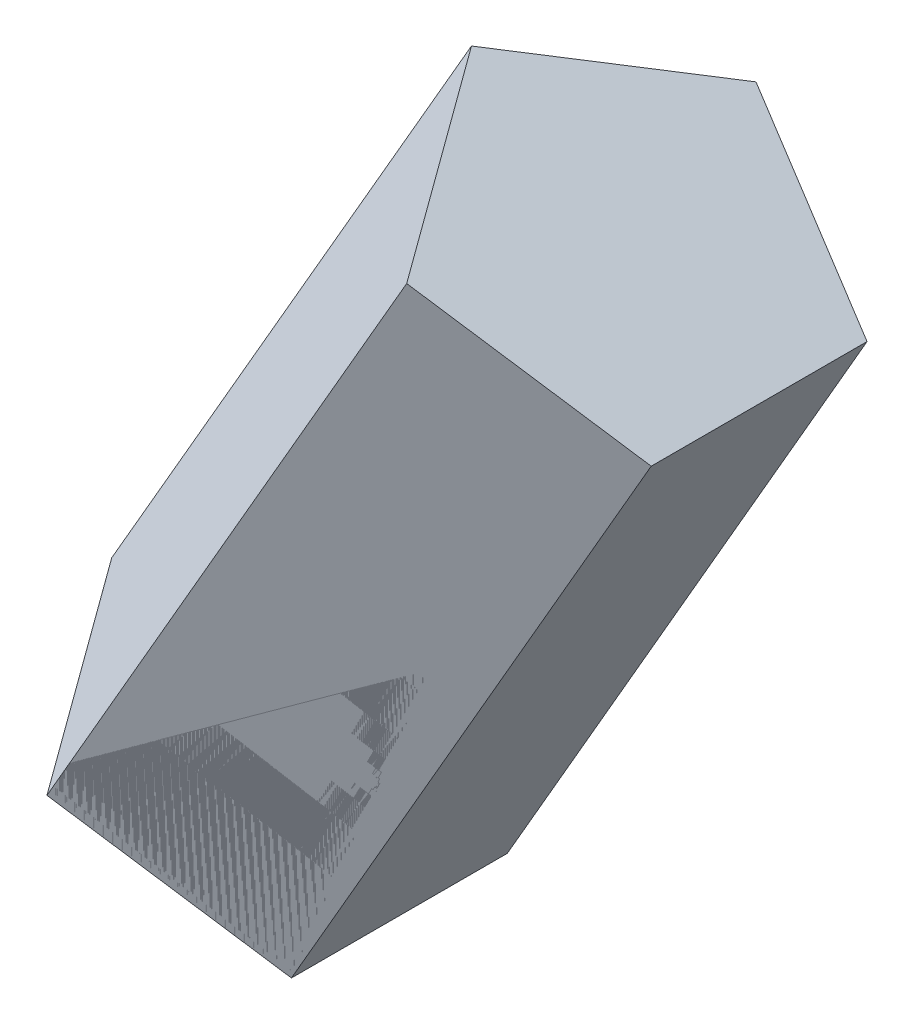
SolidWorks part; units mm, degrees
ref_plane "VP" through (0, 0, 0) normal (0, 0, 1) x (1, 0, 0)
ref_plane "HP" through (0, 0, 0) normal (0, 1, 0) x (1, 0, 0)
ref_plane "Right Plane" through (0, 0, 0) normal (1, 0, 0) x (0, 0, -1)
sketch "Sketch5" plane through (0, 0, 0) normal (0, 1, 0) x (1, 0, 0)
  line L0 (130, 0) -> (130, -60.0996) construction
  line L1 (-30.8326, 0) -> (30.8326, 0) construction
  dimension "D1" = 130
ref_plane "60 deg" through (32.5, 56.2917, 0) normal (-0.5, -0.866, 0) x (-0.866, 0.5, 0)
sketch "Sketch6" plane through (32.5, 56.2917, 0) normal (-0.5, -0.866, 0) x (-0.866, 0.5, 0)
  line L1 (-84.0516, -74.2705) -> (-66.418, -50)
  line L2 (-66.418, -50) -> (-84.0516, -25.7295)
  line L3 (-84.0516, -25.7295) -> (-112.5833, -35)
  line L4 (-112.5833, -35) -> (-112.5833, -65)
  line L5 (-112.5833, -65) -> (-84.0516, -74.2705)
  line L6 (-112.5833, 0) -> (-112.5833, -60.0996) construction
  line L7 (-30.8326, 0) -> (30.8326, 0) construction
  circle A0 centre (-91.9376, -50) radius 20.6457 construction
  dimension "D1" = 30
  dimension "D2" = 35
extrude "Boss-Extrude2" add sketch "Sketch6" against normal blind 100 contours L3 L4 L5 L1 L2
sketch "Sketch2" plane through (0, 0, 0) normal (0, 1, 0) x (1, 0, 0)
  point P0 (0, 0)
sketch "Sketch3" plane through (0, 0, 0) normal (0, 1, 0) x (1, 0, 0)
  line L0 (0, 0) -> (46.4889, -46.4889) construction
  line L1 (0, 0) -> (94.0809, 0) construction
  dimension "D1" = 45
sketch "Sketch4" plane through (0, 0, 0) normal (0, 0, 1) x (1, 0, 0)
  line L0 (0, 0) -> (93.1206, 53.7632) construction
  line L1 (0, 0) -> (46.4889, 0) construction
  dimension "D1" = 30
ref_plane "VTH" through (0, 0, 0) normal (0.4472, -0.7746, -0.4472) x (-0.8905, -0.4325, -0.1414)
other "SurfaceCut1"
sketch "Sketch7" plane through (32.5, 56.2917, 0) normal (-0.5, -0.866, 0) x (-0.866, 0.5, 0)
  line L5 (-66.418, -50) -> (-84.0516, -25.7295)
  line L6 (-84.0516, -25.7295) -> (-112.5833, -35)
  line L7 (-112.5833, -35) -> (-112.5833, -65)
  line L8 (-112.5833, -65) -> (-84.0516, -74.2705)
  line L9 (-84.0516, -74.2705) -> (-66.418, -50)
  line L10 (-66.418, -50) -> (-84.0516, -25.7295)
  line L11 (-84.0516, -25.7295) -> (-112.5833, -35)
  line L12 (-112.5833, -35) -> (-112.5833, -65)
  line L13 (-112.5833, -65) -> (-84.0516, -74.2705)
  line L14 (-84.0516, -74.2705) -> (-66.418, -50)
  dimension "D1" = 0
extrude "Boss-Extrude3" add sketch "Sketch7" against normal blind 100 separate body
ref_plane "35mm" through (0, 0, 35) normal (0, 0, 1) x (1, 0, 0)
ref_plane "Near edge" through (0, 0, 25.7295) normal (0, 0, 1) x (1, 0, 0)
ref_plane "50mm" through (0, 0, 50) normal (0, 0, 1) x (1, 0, 0)
ref_plane "65mm" through (0, 0, 65) normal (0, 0, 1) x (1, 0, 0)
ref_plane "Far edge" through (0, 0, 74.2705) normal (0, 0, 1) x (1, 0, 0)
